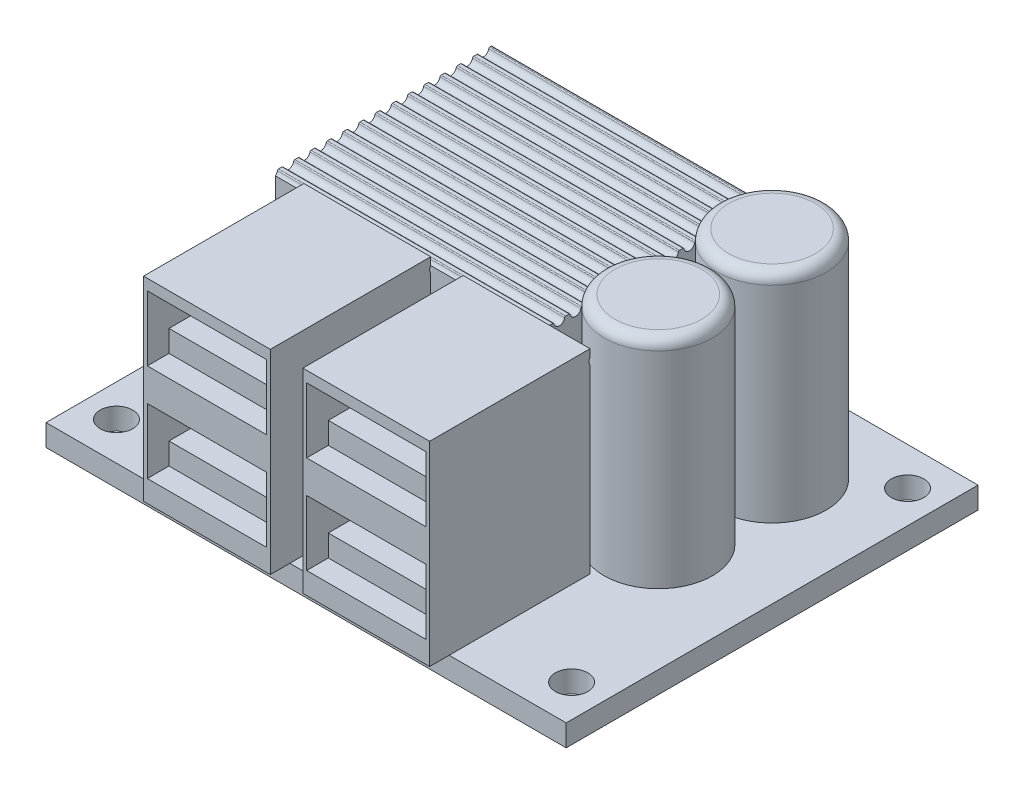
SolidWorks part; units mm, degrees
ref_plane "Front Plane" through (0, 0, 0) normal (0, 0, 1) x (1, 0, 0)
ref_plane "Top Plane" through (0, 0, 0) normal (0, 1, 0) x (1, 0, 0)
ref_plane "Right Plane" through (0, 0, 0) normal (1, 0, 0) x (0, 0, -1)
sketch "Sketch1" plane through (0, 0, 0) normal (0, 1, 0) x (1, 0, 0)
  line L1 (-24, 19) -> (24, 19)
  line L2 (-24, 19) -> (-24, -19)
  line L3 (-24, -19) -> (24, -19)
  line L4 (24, 19) -> (24, -19)
  line L5 (-24, 19) -> (24, -19) construction
  line L6 (-24, -19) -> (24, 19) construction
  circle A0 centre (-21, 15.5) radius 1.5
  circle A1 centre (-21, -15.5) radius 1.5
  circle A2 centre (21, -15.5) radius 1.5
  circle A3 centre (21, 15.5) radius 1.5
  point P0 (0, 0)
  dimension "D3" = 3
  dimension "D1" = 48
  dimension "D2" = 38
  dimension "D4" = 42
  dimension "D5" = 31
  dimension "D6" = 15.5
  dimension "D7" = 21
extrude "Boss-Extrude1" add sketch "Sketch1" along normal blind 2
sketch "Sketch2" plane through (0, 2, 0) normal (0, 1, 0) x (1, 0, 0)
  line L0 (0, 19) -> (0, -19) construction
  line L1 (24, 19) -> (-24, 19) construction
  line L2 (-24, -19) -> (24, -19) construction
  line L4 (-13.2, -6) -> (-1.5, -6)
  line L5 (-13.2, -6) -> (-13.2, -20.8)
  line L6 (-13.2, -20.8) -> (-1.5, -20.8)
  line L7 (-1.5, -6) -> (-1.5, -20.8)
  line L8 (-13.2, -6) -> (-1.5, -20.8) construction
  line L9 (-13.2, -20.8) -> (-1.5, -6) construction
  point P6 (-7.35, -13.4)
  dimension "D1" = 14.8
  dimension "D2" = 11.7
  dimension "D3" = 1.5
  dimension "D4" = 25
extrude "Boss-Extrude2" add sketch "Sketch2" along normal blind 18
sketch "Sketch3" plane through (0, 0, 20.8) normal (0, 0, 1) x (1, 0, 0)
  line L0 (-7.35, 20) -> (-7.35, 2) construction
  line L1 (-13.2, 20) -> (-1.5, 20) construction
  line L2 (-13.2, 2) -> (-1.5, 2) construction
  line L4 (-1.85, 13) -> (-12.85, 13)
  line L5 (-1.85, 13) -> (-1.85, 19)
  line L6 (-1.85, 19) -> (-12.85, 19)
  line L7 (-12.85, 13) -> (-12.85, 19)
  line L8 (-1.85, 13) -> (-12.85, 19) construction
  line L9 (-1.85, 19) -> (-12.85, 13) construction
  line L10 (-12.85, 10) -> (-1.85, 10)
  line L11 (-12.85, 10) -> (-12.85, 4)
  line L12 (-12.85, 4) -> (-1.85, 4)
  line L13 (-1.85, 10) -> (-1.85, 4)
  line L14 (-12.85, 10) -> (-1.85, 4) construction
  line L15 (-12.85, 4) -> (-1.85, 10) construction
  point P6 (-7.35, 16)
  point P11 (-7.35, 7)
  dimension "D1" = 11
  dimension "D2" = 6
  dimension "D3" = 1
  dimension "D4" = 3
extrude "Cut-Extrude1" cut sketch "Sketch3" against normal blind 13
sketch "Sketch4" plane through (0, 13, 0) normal (0, 1, 0) x (1, 0, 0)
  line L0 (-12.85, -7.8) -> (-12.85, -20.8) construction
  line L1 (-1.85, -7.8) -> (-1.85, -20.8) construction
  line L2 (-12.85, -7.8) -> (-12.85, -18.8)
  line L3 (-1.85, -7.8) -> (-1.85, -18.8)
  line L4 (-12.85, -7.8) -> (-1.85, -7.8) construction
  line L5 (-12.85, -7.8) -> (-1.85, -7.8)
  line L6 (-12.85, -18.8) -> (-1.85, -18.8)
  dimension "D1" = 11
extrude "Boss-Extrude3" add sketch "Sketch4" along normal blind 2
sketch "Sketch5" plane through (0, 4, 0) normal (0, 1, 0) x (1, 0, 0)
  line L0 (-12.85, -7.8) -> (-12.85, -20.8) construction
  line L1 (-12.85, -7.8) -> (-1.85, -7.8) construction
  line L2 (-1.85, -7.8) -> (-1.85, -20.8) construction
  line L3 (-12.85, -7.8) -> (-12.85, -18.8)
  line L4 (-12.85, -7.8) -> (-1.85, -7.8)
  line L5 (-1.85, -7.8) -> (-1.85, -18.8)
  line L6 (-12.85, -18.8) -> (-1.85, -18.8)
  dimension "D1" = 11
extrude "Boss-Extrude4" add sketch "Sketch5" along normal blind 2
mirror "Mirror1" about plane through (0, 0, 0) normal (1, 0, 0) of "Boss-Extrude4", "Boss-Extrude3", "Cut-Extrude1", "Boss-Extrude2"
sketch "Sketch6" plane through (0, 2, 0) normal (0, 1, 0) x (1, 0, 0)
  line L1 (-16.5363, 14.7) -> (8.4637, 14.7)
  line L2 (-16.5363, 14.7) -> (-16.5363, -5.3)
  line L3 (-16.5363, -5.3) -> (8.4637, -5.3)
  line L4 (8.4637, 14.7) -> (8.4637, -5.3)
  line L5 (-16.5363, 14.7) -> (8.4637, -5.3) construction
  line L6 (-16.5363, -5.3) -> (8.4637, 14.7) construction
  line L7 (24, 19) -> (-24, 19) construction
  line L8 (-24, 19) -> (-24, -19) construction
  point P0 (-4.0363, 4.7)
  dimension "D3" = 25
  dimension "D4" = 20
  dimension "D7" = 7.4637
  dimension "D8" = 4.3
extrude "Boss-Extrude5" add sketch "Sketch6" along normal blind 17
sketch "Sketch7" plane through (-16.5363, 0, 0) normal (-1, 0, 0) x (0, 0, 1)
  line L0 (-14.7, 19) -> (5.3, 19) construction
  line L1 (-14.7, 19) -> (-14.7, 2) construction
  circle A0 centre (-13.9013, 19) radius 0.5
  circle A1 centre (-12.4013, 19) radius 0.5
  circle A2 centre (-10.9013, 19) radius 0.5
  circle A3 centre (-9.4013, 19) radius 0.5
  circle A4 centre (-7.9013, 19) radius 0.5
  circle A5 centre (-6.4013, 19) radius 0.5
  circle A6 centre (-4.9013, 19) radius 0.5
  circle A7 centre (-3.4013, 19) radius 0.5
  circle A8 centre (-1.9013, 19) radius 0.5
  circle A9 centre (-0.4013, 19) radius 0.5
  circle A10 centre (1.0987, 19) radius 0.5
  circle A11 centre (2.5987, 19) radius 0.5
  circle A12 centre (4.0987, 19) radius 0.5
  circle A13 centre (5.5987, 19) radius 0.5
  dimension "D1" = 1
  dimension "D2" = 0.7987
  dimension "D3" = 14
extrude "Cut-Extrude2" cut sketch "Sketch7" against normal through all
fillet "Fillet1" radius 0.1 28 edges at (-4.0363, 19, -14.7) (-4.0363, 19, 5.0987) (-4.0363, 19, 3.5987) (-4.0363, 19, 4.5987) (-4.0363, 19, 2.0987) (-4.0363, 19, 3.0987) (-4.0363, 19, 0.5987) (-4.0363, 19, 1.5987) (-4.0363, 19, -0.9013) (-4.0363, 19, 0.0987) (-4.0363, 19, -2.4013) (-4.0363, 19, -1.4013) (-4.0363, 19, -3.9013) (-4.0363, 19, -2.9013) (-4.0363, 19, -5.4013) (-4.0363, 19, -4.4013) (-4.0363, 19, -6.9013) (-4.0363, 19, -5.9013) (-4.0363, 19, -8.4013) (-4.0363, 19, -7.4013) (-4.0363, 19, -9.9013) (-4.0363, 19, -8.9013) (-4.0363, 19, -11.4013) (-4.0363, 19, -10.4013) (-4.0363, 19, -12.9013) (-4.0363, 19, -11.9013) (-4.0363, 19, -14.4013) (-4.0363, 19, -13.4013)
sketch "Sketch8" plane through (0, 2, 0) normal (0, 1, 0) x (1, 0, 0)
  line L1 (24, -19) -> (24, 19) construction
  line L2 (24, 19) -> (-24, 19) construction
  circle A0 centre (14, 10) radius 5
  circle A1 centre (14, -0.5) radius 5
  dimension "D1" = 10
  dimension "D2" = 9
  dimension "D3" = 10.5
  dimension "D4" = 10
extrude "Boss-Extrude6" add sketch "Sketch8" along normal blind 20
fillet "Fillet2" radius 1 2 edges at (14, 22, -5) (14, 22, 5.5)
sketch "Sketch9" plane through (0, 2, 0) normal (0, 1, 0) x (1, 0, 0)
  line L0 (-24, 19) -> (-24, -19) construction
  line L1 (-23.2607, 7) -> (-18.2607, 7)
  line L2 (-23.2607, 7) -> (-23.2607, -8)
  line L3 (-23.2607, -8) -> (-18.2607, -8)
  line L4 (-18.2607, 7) -> (-18.2607, -8)
  line L5 (-23.2607, 7) -> (-18.2607, -8) construction
  line L6 (-23.2607, -8) -> (-18.2607, 7) construction
  line L7 (24, 19) -> (-24, 19) construction
  point P0 (-20.7607, -0.5)
  dimension "D1" = 5
  dimension "D2" = 0.7393
  dimension "D3" = 15
  dimension "D4" = 12
extrude "Boss-Extrude7" add sketch "Sketch9" along normal blind 7
chamfer "Chamfer1" distance 2 angle 45 1 edges at (-18.2607, 9, 0.5)
sketch "Sketch10" plane through (0, 9, 0) normal (0, 1, 0) x (1, 0, 0)
  line L1 (-23.2607, 7) -> (-23.2607, -8) construction
  circle A0 centre (-21.9526, 3.5) radius 1
  circle A1 centre (-21.9526, -4.5) radius 1
  point P6 (-23.2607, -0.5)
  dimension "D1" = 2
  dimension "D2" = 8
  dimension "D3" = 4
extrude "Cut-Extrude3" cut sketch "Sketch10" against normal blind 1
